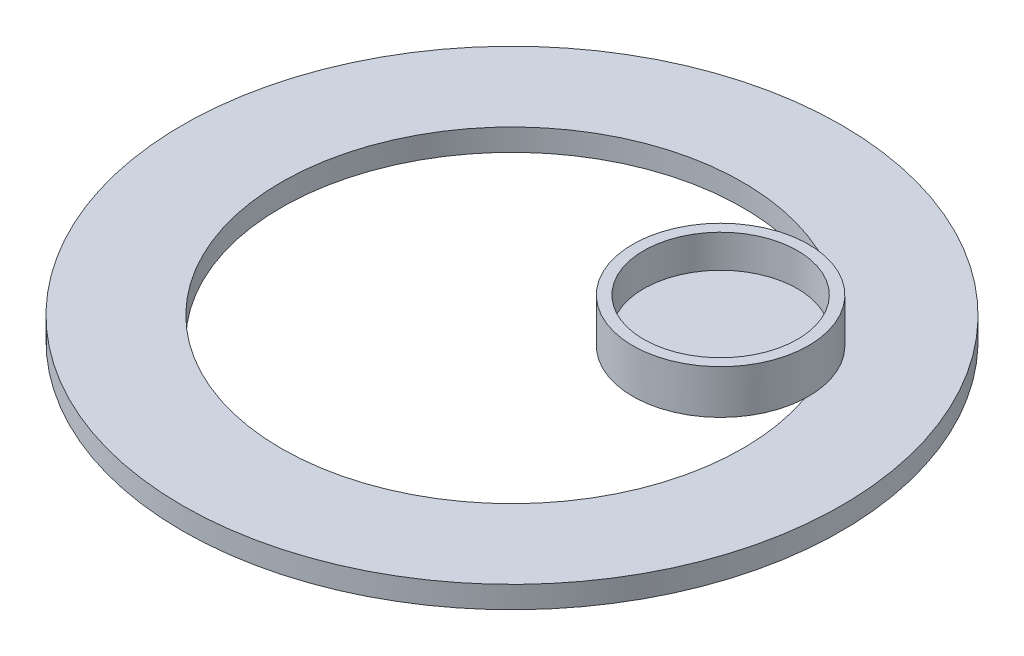
SolidWorks part; units mm, degrees
ref_plane "Front Plane" through (0, 0, 0) normal (0, 0, 1) x (1, 0, 0)
ref_plane "Top Plane" through (0, 0, 0) normal (0, 1, 0) x (1, 0, 0)
ref_plane "Right Plane" through (0, 0, 0) normal (1, 0, 0) x (0, 0, -1)
sketch "Sketch1" plane through (0, 0, 0) normal (0, 1, 0) x (1, 0, 0)
  circle A0 centre (0, 0) radius 30
extrude "Boss-Extrude1" add sketch "Sketch1" along normal blind 2
sketch "Sketch2" plane through (0, 2, 0) normal (0, 1, 0) x (1, 0, 0)
  circle A1 centre (0, 0) radius 21
extrude "Cut-Extrude1" cut sketch "Sketch2" against normal blind 2
sketch "Sketch3" plane through (0, 2, 0) normal (0, 1, 0) x (1, 0, 0)
  circle A0 centre (11.8907, 7.0984) radius 8
extrude "Boss-Extrude2" add sketch "Sketch3" along normal blind 4
sketch "Sketch4" plane through (0, 6, 0) normal (0, 1, 0) x (1, 0, 0)
  circle A0 centre (11.8907, 7.0984) radius 7
extrude "Cut-Extrude2" cut sketch "Sketch4" against normal blind 3
sketch "Sketch6" plane through (0, 2, 0) normal (0, 1, 0) x (1, 0, 0)
  arc A0 (2.9657, 28.16) -> (24.104, -14.8586) centre (0, 0) cw
  text T0 "HELLO  SUNSHINE" font "Century Gothic" height in points 16
  point P4 (24.3525, -15.0118)
  point P5 (2.9657, 28.16)
  point P7 (0, 0)
  point P8 (0, 0)
